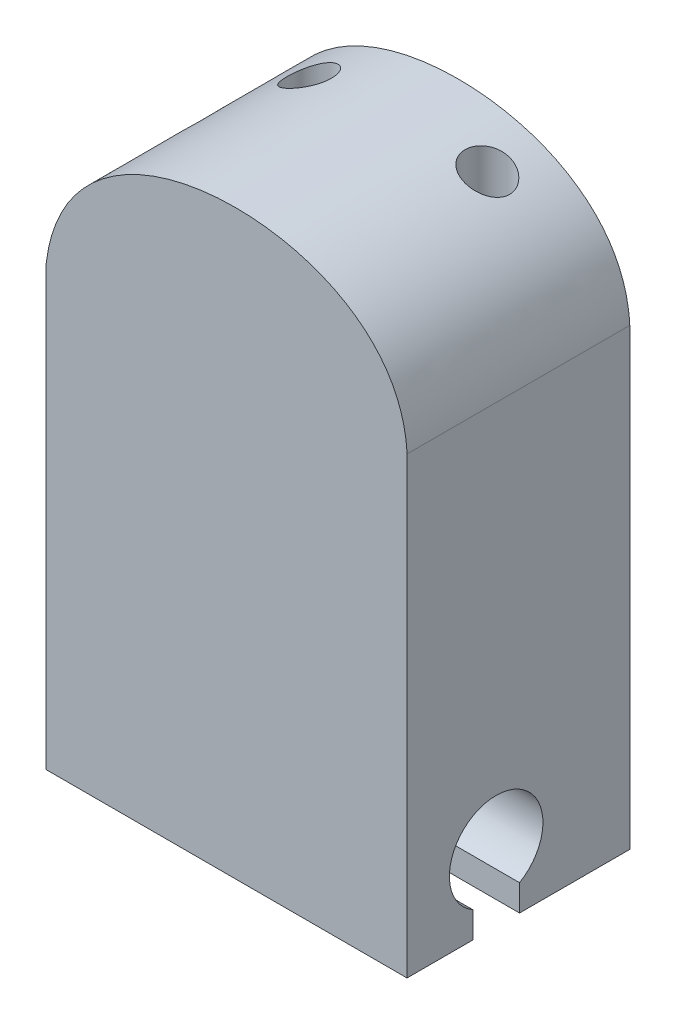
SolidWorks part; units mm, degrees
ref_plane "Front Plane" through (0, 0, 0) normal (0, 0, 1) x (1, 0, 0)
ref_plane "Top Plane" through (0, 0, 0) normal (0, 1, 0) x (1, 0, 0)
ref_plane "Right Plane" through (0, 0, 0) normal (1, 0, 0) x (0, 0, -1)
sketch "Sketch1" plane through (0, 0, 0) normal (0, 0, 1) x (1, 0, 0)
  line L0 (8.1, 0) -> (-8.1, 0)
  line L1 (0, 41.8397) -> (0, -28.0151) construction
  line L2 (-8.1, 0) -> (-8.1, 24)
  line L3 (-8.1, 24) -> (8.1, 24)
  line L4 (8.1, 24) -> (8.1, 0)
  spline S0 degree 3 poles (-8.1, 19.7) (-7.5966, 23.8813) (-0.1224, 28.1142) (8.3234, 24.3049) (8.1, 19.7) knots 0 0 0 0 0.492427 1 1 1 1
  point P6 (0, 0)
  dimension "D1" = 8.1
  dimension "D2" = 24
  dimension "D3" = 4.3
  dimension "D4" = 4.3
  dimension "D5" = 6.4
extrude "Boss-Extrude1" add sketch "Sketch1" along normal blind 10 contours L1 L3 S0 L2 L0 | L3 L1 L0 L4 S0 | L1 S0 L3 | S0 L1 L3
sketch "Sketch11" plane through (0, 0, 0) normal (0, -1, 0) x (1, 0, 0)
  line L0 (-8.1, 10) -> (-8.1, 0) construction
  line L4 (-8.1, 2.2959) -> (-8.1, 4.5918)
  line L5 (8.1, 2.2959) -> (-8.6978, 2.2959) construction
  line L6 (0, 0) -> (0, 6.168) construction
  circle A0 centre (4, 2.2959) radius 1
  circle A1 centre (-4, 2.2959) radius 1
  dimension "D2" = 2
  dimension "D1" = 4
extrude "Cut-Extrude9" cut sketch "Sketch11" against normal up to surface (25.0646 mm away) contours A0 | A1
ref_plane "Plane1" through (0, 0, 0) normal (-1, 0, 0) x (0, 0, 1)
sketch "Sketch14" plane through (0, 0, 0) normal (-1, 0, 0) x (0, 0, 1)
  line L0 (4.95, 0) -> (7.05, 0)
  line L1 (10, 0) -> (0, 0) construction
  line L2 (6, 3) -> (6, -2.0344) construction
  line L3 (7.05, 0) -> (7.05, 1.1813)
  line L5 (4.95, 0) -> (4.95, 1.1813)
  circle A0 centre (6, 3) radius 2.1
  point P10 (6, 0)
  dimension "D1" = 4.2
  dimension "D3" = 3
  dimension "D4" = 1.05
extrude "Cut-Extrude16" cut sketch "Sketch14" against normal blind 14.1 and the other way blind 14.1
